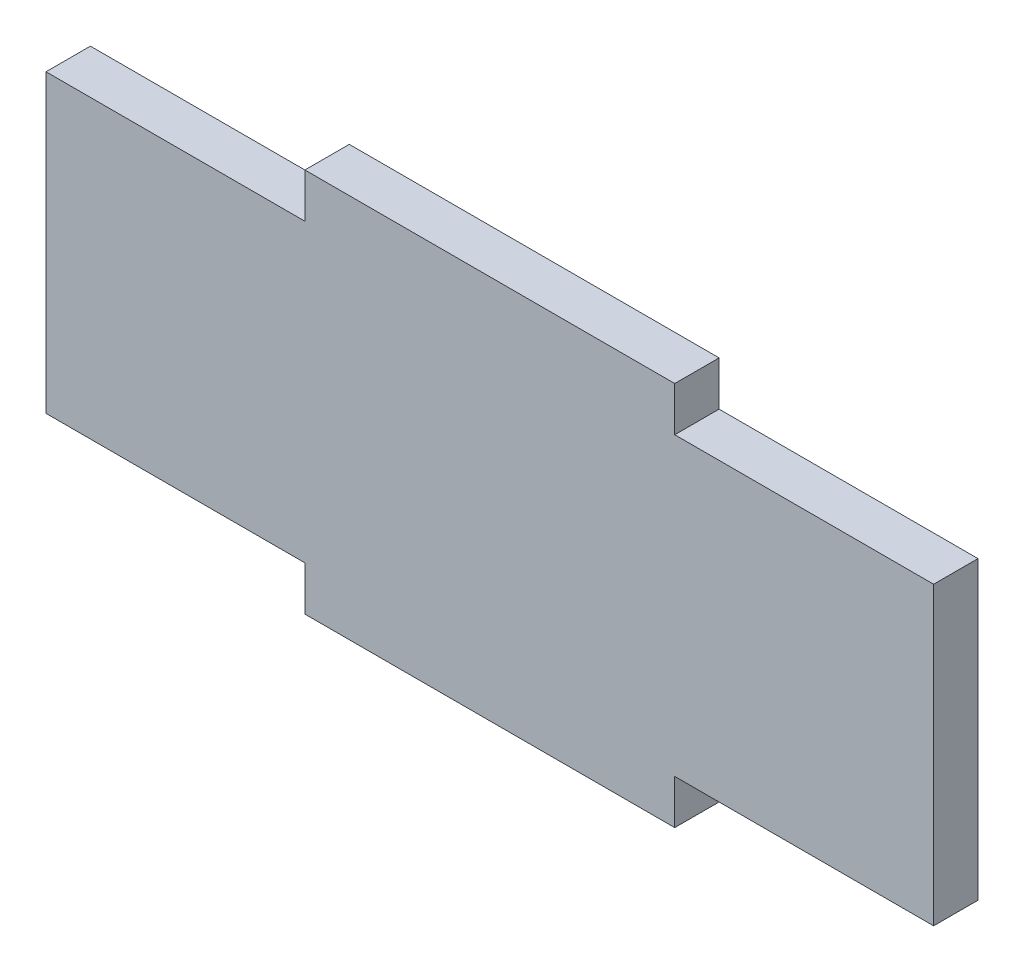
SolidWorks part; units mm, degrees
ref_plane "Plan de face" through (0, 0, 0) normal (0, 0, 1) x (1, 0, 0)
ref_plane "Plan de dessus" through (0, 0, 0) normal (0, 1, 0) x (1, 0, 0)
ref_plane "Plan de droite" through (0, 0, 0) normal (1, 0, 0) x (0, 0, -1)
sketch "Esquisse1" plane through (0, 0, 0) normal (0, 0, 1) x (1, 0, 0)
  line L1 (60, 20) -> (-60, 20)
  line L2 (60, 20) -> (60, -20)
  line L3 (60, -20) -> (-60, -20)
  line L4 (-60, 20) -> (-60, -20)
  line L5 (60, 20) -> (-60, -20) construction
  line L6 (60, -20) -> (-60, 20) construction
  point P0 (0, 0)
  dimension "D1" = 120
  dimension "D2" = 40
extrude "Boss.-Extru.1" add sketch "Esquisse1" along normal blind 6
sketch "Esquisse2" plane through (0, 0, 6) normal (0, 0, 1) x (1, 0, 0)
  line L0 (60, 20) -> (-60, 20) construction
  line L1 (-25, 20) -> (25, 20)
  line L2 (-25, 20) -> (-25, 26)
  line L3 (-25, 26) -> (25, 26)
  line L4 (25, 20) -> (25, 26)
  line L5 (-60, 20) -> (-60, -20) construction
  line L6 (60, -20) -> (60, 20) construction
  line L7 (-60, 0) -> (60, 0) construction
  line L8 (-25, -26) -> (25, -26)
  line L9 (25, -20) -> (25, -26)
  line L10 (-25, -20) -> (25, -20)
  line L11 (-25, -20) -> (-25, -26)
  dimension "D1" = 50
  dimension "D2" = 35
  dimension "D3" = 6
extrude "Boss.-Extru.2" add sketch "Esquisse2" against normal blind 6
